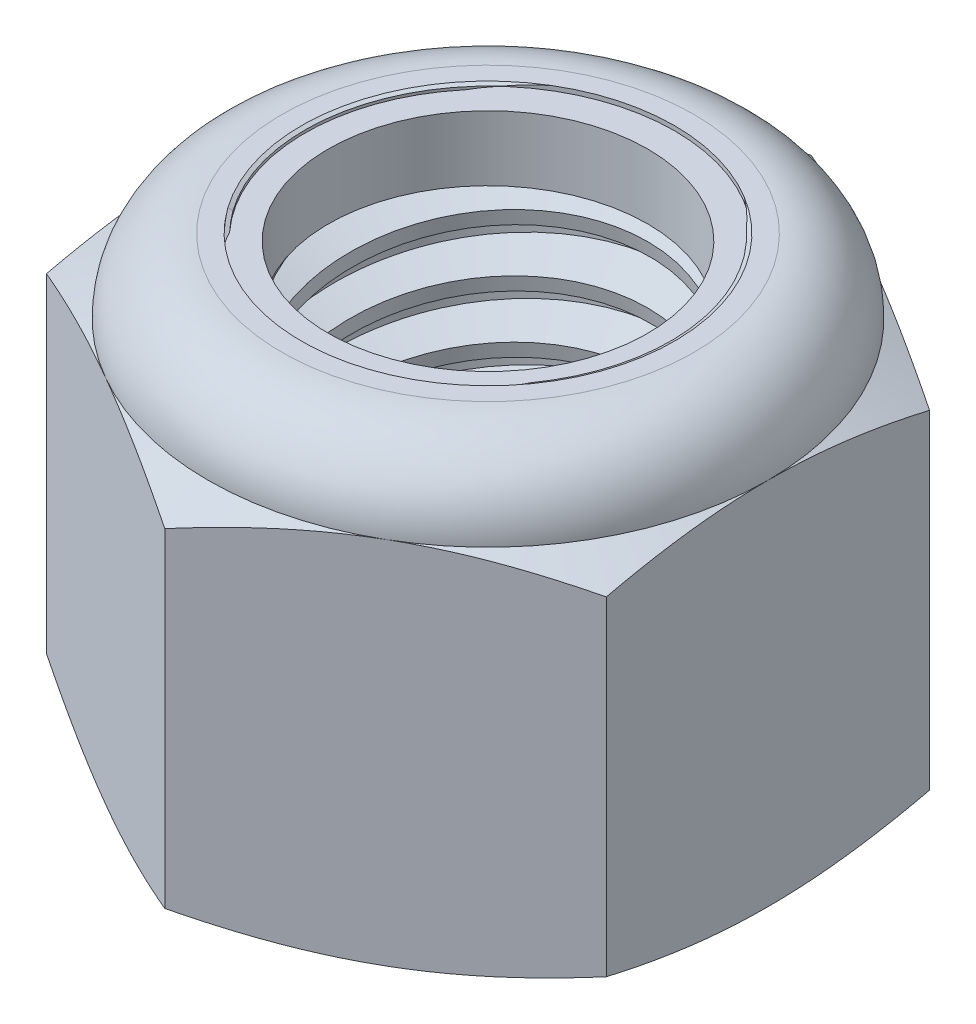
SolidWorks part; units mm, degrees
ref_plane "Front" through (0, 0, 0) normal (0, 0, 1) x (1, 0, 0)
ref_plane "Top" through (0, 0, 0) normal (0, 1, 0) x (1, 0, 0)
ref_plane "Right" through (0, 0, 0) normal (1, 0, 0) x (0, 0, -1)
sketch "Sketch1" plane through (0, 0, 0) normal (0, 1, 0) x (1, 0, 0)
  line L1 (0, 10.9985) -> (-9.525, 5.4993)
  line L2 (-9.525, 5.4993) -> (-9.525, -5.4993)
  line L3 (-9.525, -5.4993) -> (0, -10.9985)
  line L4 (0, -10.9985) -> (9.525, -5.4993)
  line L5 (9.525, -5.4993) -> (9.525, 5.4993)
  line L6 (9.525, 5.4993) -> (0, 10.9985)
  circle A0 centre (0, 0) radius 9.525 construction
  dimension "Hex Flats" = 19.05
extrude "Extrude1" add sketch "Sketch1" along normal blind 15.0812
sketch "Sketch2" plane through (0, 0, 0) normal (1, 0, 0) x (0, 0, -1)
  line L0 (-6.35, 0) -> (-6.35, 15.0812) construction
  line L1 (0, 0) -> (6.35, 0)
  line L2 (0, 0) -> (0, 15.0812)
  line L3 (0, 15.0812) -> (6.35, 15.0812)
  line L4 (6.35, 0) -> (6.35, 15.0812)
  line L5 (-5.4993, 15.0812) -> (5.4993, 15.0812) construction
  line L7 (0, -6.35) -> (0, 0) construction
  dimension "Thread Dia" = 12.7
revolve "Revolve1" add sketch "Sketch2" angle 360 about L7
sketch "Sketch3" plane through (0, 0, 0) normal (1, 0, 0) x (0, 0, -1)
  line L0 (6.35, 15.0812) -> (-6.35, 15.0812) construction
  line L1 (-6.35, 15.0812) -> (-6.35, 13.1274) construction
  line L2 (-6.35, 13.1274) -> (6.35, 15.0812) construction
  line L3 (6.35, 15.0812) -> (6.3871, 14.8399) construction
  line L4 (6.3871, 14.8399) -> (6.6471, 13.1501)
  line L5 (6.6471, 13.1501) -> (5.509, 13.5928)
  line L6 (5.509, 13.5928) -> (5.4347, 14.0756)
  line L7 (5.4347, 14.0756) -> (6.3871, 14.8399)
  line L8 (5.4719, 13.8342) -> (6.5171, 13.995) construction
  line L9 (6.35, 15.0812) -> (6.35, 13.9693) construction
  line L10 (6.35, 13.9693) -> (-6.35, 12.0154) construction
  line L11 (-6.35, 12.0154) -> (-6.35, 13.1274) construction
  line L12 (-0.3214, 15.0812) -> (0.3214, 10.9035) construction
  line L13 (-6.35, 0) -> (-6.35, 15.0812) construction
  line L14 (0, 15.0812) -> (6.35, 15.0812) construction
  line L15 (6.35, 0) -> (6.35, 15.0812) construction
  point P13 (0, 12.9924)
  dimension "D1" = 0.2442
  dimension "D2" = 0.4885
  dimension "Thread Pitch" = 1.9538
  dimension "D4" = 60
  dimension "D5" = 1.9538
revolve "Cut-Revolve1" cut sketch "Sketch3" angle 360 about L12
pattern_linear "LPattern1" count 8 spacing 1.9538 along (0, -1, 0) count 2 spacing 1.9538 along (0, 1, 0) of "Cut-Revolve1"
sketch "Sketch4" plane through (0, 0, 0) normal (1, 0, 0) x (0, 0, -1)
  line L0 (0, 15.0812) -> (6.35, 15.0812)
  line L1 (6.35, 15.0812) -> (5.4347, 14.6545)
  line L2 (5.4347, 14.6545) -> (5.4347, 0.4268)
  line L3 (5.4347, 0.4268) -> (6.35, 0)
  line L4 (6.35, 0) -> (0, 0)
  line L5 (0, 0) -> (0, 15.0812)
  line L6 (6.35, 0) -> (6.35, 15.0812) construction
  line L7 (0, 15.0812) -> (6.35, 15.0812) construction
  line L8 (0, 0) -> (6.35, 0) construction
  line L9 (0, 0) -> (0, 15.0812) construction
  line L10 (0, 15.0812) -> (0, 16.0911) construction
  dimension "D1" = 25
revolve "Cut-Revolve2" cut sketch "Sketch4" angle 360 about L10
combine bodies "Combine1" operation type subtract main body 112 bodies to subtract 111
sketch "Sketch5" plane through (0, 0, 0) normal (1, 0, 0) x (0, 0, -1)
  line L0 (0, 0) -> (9.525, 0)
  line L1 (9.525, 0) -> (10.9985, 0.6871)
  line L2 (10.9985, 0.6871) -> (10.9985, 11.8806)
  line L3 (10.9985, 11.8806) -> (9.525, 12.5677)
  line L4 (7.0115, 15.0812) -> (7.0115, 16.3512)
  line L5 (7.0115, 16.3512) -> (12.2685, 16.3512)
  line L6 (12.2685, 16.3512) -> (12.2685, -1.27)
  line L7 (12.2685, -1.27) -> (0, -1.27)
  line L8 (0, -1.27) -> (0, 0)
  line L9 (9.525, 12.5677) -> (9.525, 0) construction
  line L10 (0, 0) -> (6.35, 0) construction
  line L13 (10.9985, 6.2839) -> (12.2685, 6.2839) construction
  line L14 (10.9985, 15.0812) -> (10.9985, 0) construction
  line L15 (0, 0) -> (0, 16.3512) construction
  line L20 (0, 16.3512) -> (7.0115, 16.3512) construction
  line L22 (0, 15.0812) -> (6.35, 15.0812) construction
  arc A0 (9.525, 12.5677) -> (7.0115, 15.0812) centre (7.0115, 12.5677) ccw
  dimension "D1" = 25
  dimension "D2" = 1.27
  dimension "D3" = 15.0812
  dimension "D4" = 2.5135
revolve "Cut-Revolve3" cut sketch "Sketch5" angle 360 about L15
sketch "Sketch6" plane through (0, 0, 0) normal (1, 0, 0) x (0, 0, -1)
  line L0 (0, 12.5677) -> (9.3726, 12.5677)
  line L1 (7.0115, 14.9288) -> (6.2231, 14.9288)
  line L2 (0, 16.3512) -> (0, 12.5677)
  line L3 (6.2231, 16.3512) -> (0, 16.3512)
  line L4 (0, 16.3512) -> (7.0115, 16.3512) construction
  line L5 (0, 0) -> (0, 16.3512) construction
  line L6 (0, 16.3512) -> (0, 44.323) construction
  line L7 (6.2231, 14.9288) -> (6.2231, 16.3512)
  line L8 (7.0115, 15.0812) -> (7.0115, 14.9288) construction
  line L9 (6.2231, 14.9288) -> (5.4347, 14.9288) construction
  line L10 (5.4347, 14.9288) -> (5.4347, 14.6545) construction
  arc A0 (9.3726, 12.5677) -> (7.0115, 14.9288) centre (7.0115, 12.5677) ccw
  arc A1 (9.525, 12.5677) -> (7.0115, 15.0812) centre (7.0115, 12.5677) ccw construction
  dimension "D1" = 0.1524
revolve "Cut-Revolve4" cut sketch "Sketch6" angle 360 about L6
sketch "Sketch7" plane through (0, 0, 0) normal (1, 0, 0) x (0, 0, -1)
  line L0 (5.4347, 12.6439) -> (9.2951, 12.6439)
  line L1 (7.0115, 14.8526) -> (5.4347, 14.8526)
  line L2 (5.4347, 14.8526) -> (5.4347, 12.6439)
  line L3 (5.4347, 12.6439) -> (0, 12.6439) construction
  line L4 (0, 12.6439) -> (0, 14.8526) construction
  line L5 (0, 14.8526) -> (5.4347, 14.8526) construction
  line L6 (5.4347, 12.6439) -> (5.4347, 12.5677) construction
  line L7 (0, 12.5677) -> (9.3726, 12.5677) construction
  line L8 (7.0115, 14.8526) -> (7.0115, 14.9288) construction
  arc A0 (9.2951, 12.6439) -> (7.0115, 14.8526) centre (7.0115, 12.5677) ccw
  arc A2 (9.3726, 12.5677) -> (7.0115, 14.9288) centre (7.0115, 12.5677) ccw construction
  dimension "D1" = 0.0762
revolve "Revolve2" add sketch "Sketch7" angle 360 about L4
equation "\"D1@Sketch3\"=\"Thread Pitch@Sketch3\"/8"
equation "\"D2@Sketch3\"=\"Thread Pitch@Sketch3\"/4"
equation "\"D5@Sketch3\"=\"Thread Pitch@Sketch3\""
equation "\"D4@LPattern1\"=\"Thread Pitch@Sketch3\""
equation "\"D3@LPattern1\"=\"Thread Pitch@Sketch3\""
equation "\"D1@LPattern1\"=\"Height@Extrude1\"/\"Thread Pitch@Sketch3\""
equation "\"D4@Sketch5\"=\"Height@Extrude1\"/6"
